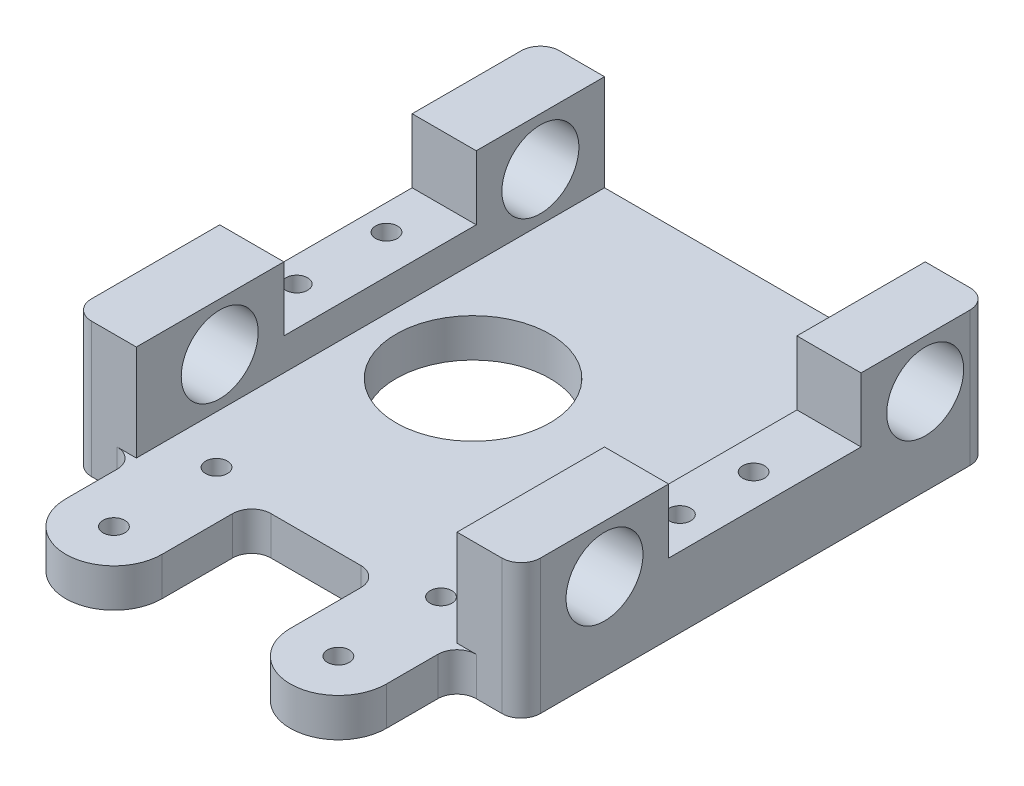
SolidWorks part; units mm, degrees
ref_plane "Plan de face" through (0, 0, 0) normal (0, 0, 1) x (1, 0, 0)
ref_plane "Plan de dessus" through (0, 0, 0) normal (0, 1, 0) x (1, 0, 0)
ref_plane "Plan de droite" through (0, 0, 0) normal (1, 0, 0) x (0, 0, -1)
sketch "Esquisse1" plane through (0, 0, 0) normal (0, 1, 0) x (1, 0, 0)
  line L0 (0, 0) -> (70, 0)
  line L1 (70, 0) -> (70, -73)
  line L2 (70, -73) -> (60, -73)
  line L3 (60, -73) -> (60, -84)
  line L4 (45, -84) -> (45, -70)
  line L5 (45, -70) -> (25, -70)
  line L6 (25, -70) -> (25, -84)
  line L7 (10, -84) -> (10, -73)
  line L8 (10, -73) -> (0, -73)
  line L9 (0, -73) -> (0, 0)
  arc A0 (60, -84) -> (45, -84) centre (52.5, -84) cw
  arc A1 (25, -84) -> (10, -84) centre (17.5, -84) cw
  circle A2 centre (25.5, -36) radius 12
  dimension "D2" = 36
  dimension "D3" = 25.5
  dimension "D4" = 24
  dimension "D10" = 84
  dimension "D1" = 70
  dimension "D5" = 73
  dimension "D6" = 70
  dimension "D7" = 17.5
  dimension "D8" = 10
  dimension "D9" = 52.5
extrude "Boss.-Extru.1" add sketch "Esquisse1" along normal blind 6
sketch "Esquisse3" plane through (0, 6, 0) normal (0, 1, 0) x (1, 0, 0)
  line L1 (0, 0) -> (10, 0)
  line L2 (0, 0) -> (0, -73)
  line L3 (0, -73) -> (10, -73)
  line L4 (10, 0) -> (10, -73)
  line L5 (70, 0) -> (60, 0)
  line L6 (70, 0) -> (70, -73)
  line L7 (70, -73) -> (60, -73)
  line L8 (60, 0) -> (60, -73)
extrude "Boss.-Extru.2" add sketch "Esquisse3" along normal blind 15
sketch "Esquisse4" plane through (0, 0, 0) normal (1, 0, 0) x (0, 0, -1)
  line L0 (-73, 21) -> (0, 21) construction
  line L1 (-20, 21) -> (-50, 21)
  line L2 (-20, 21) -> (-20, 11)
  line L3 (-20, 11) -> (-50, 11)
  line L4 (-50, 21) -> (-50, 11)
  line L5 (0, 21) -> (0, 0) construction
  line L6 (-73, 0) -> (0, 0) construction
  circle A0 centre (-60, 13.5) radius 6
  circle A1 centre (-10, 13.5) radius 6
  dimension "D3" = 12
  dimension "D1" = 30
  dimension "D2" = 20
  dimension "D4" = 11
  dimension "D5" = 10
  dimension "D6" = 60
  dimension "D7" = 13.5
extrude "Enlèv. mat.-Extru.1" cut sketch "Esquisse4" along normal through all
hole_wizard "Dégagement M32" positions "Esquisse7" profile "Esquisse8" hole size "M3" standard "ISO" end condition up to next
sketch "Esquisse7" plane through (0, 11, 0) normal (0, 1, 0) x (1, 0, 0)
  line L2 (60, 0) -> (10, 0) construction
  line L3 (0, 0) -> (0, -20) construction
  line L4 (70, 0) -> (60, 0) construction
  point P0 (4, -28)
  point P2 (4, -42)
  point P4 (17.5, -84)
  point P7 (52.5, -84)
  point P10 (17.5, -68)
  point P12 (52.5, -68)
  point P14 (65, -31.75)
  point P16 (65, -43.25)
  dimension "D1" = 28
  dimension "D2" = 42
  dimension "D3" = 68
  dimension "D4" = 4
  dimension "D5" = 65
  dimension "D6" = 31.75
  dimension "D7" = 43.25
sketch "Esquisse8" plane through (4, 11, 28) normal (1, 0, 0) x (0, 0, 1)
  line L0 (0, 0) -> (0, 11)
  line L1 (0, 11) -> (1.7, 11)
  line L2 (1.7, 11) -> (1.7, 0)
  line L5 (1.7, 0) -> (0, 0)
  line L11 (0, -6.35) -> (0, 107.95) construction
  dimension "Diamètre du perçage jusqu'au prochain" = 3.4
  dimension "Profondeur du perçage jusqu'au prochain" = 11
fillet "Congé2" radius 3 8 edges at (0, 10.5, 73) (10, 3, 73) (25, 3, 70) (45, 3, 70) (60, 3, 73) (70, 10.5, 0) (0, 10.5, 0) (70, 10.5, 73)
